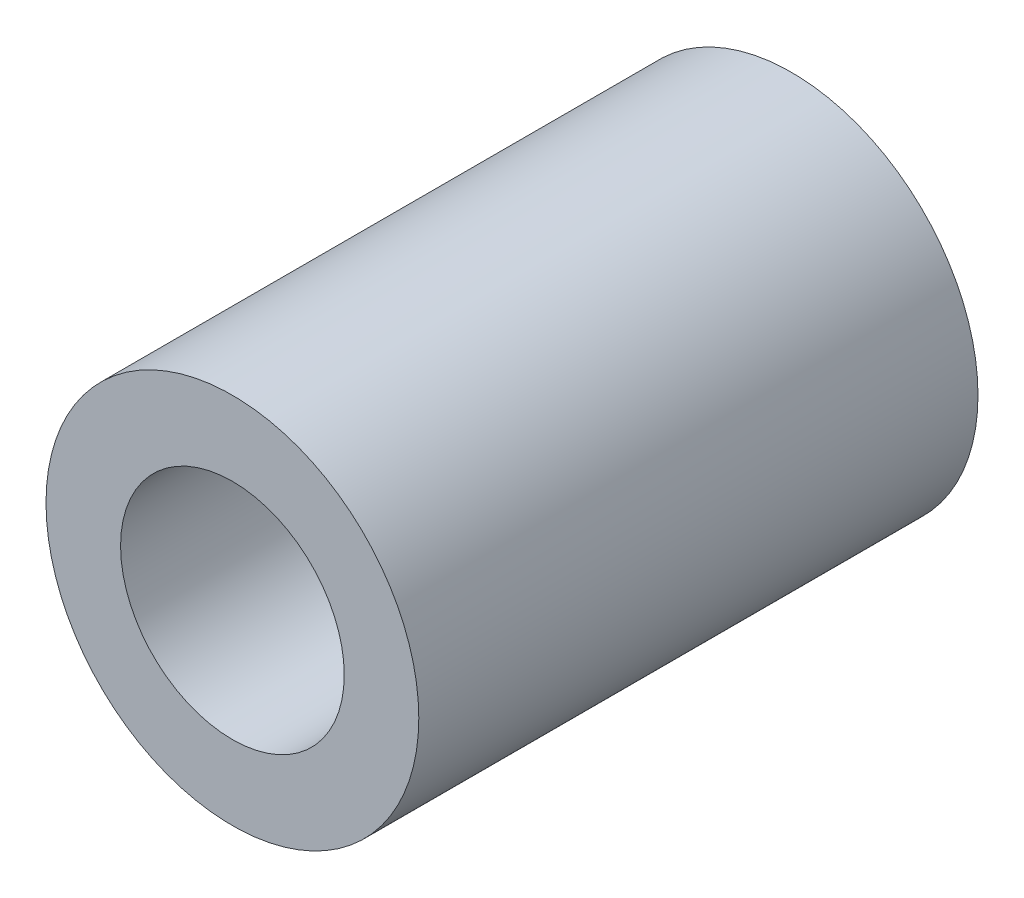
SolidWorks part; units mm, degrees
ref_plane "Plan de face" through (0, 0, 0) normal (0, 0, 1) x (1, 0, 0)
ref_plane "Plan de dessus" through (0, 0, 0) normal (0, 1, 0) x (1, 0, 0)
ref_plane "Plan de droite" through (0, 0, 0) normal (1, 0, 0) x (0, 0, -1)
sketch "Esquisse1" plane through (0, 0, 0) normal (0, 0, 1) x (1, 0, 0)
  circle A0 centre (0, 0) radius 1.2
  circle A1 centre (0, 0) radius 2
  dimension "D1" = 4
  dimension "D2" = 2.4
extrude "Boss.-Extru.1" add sketch "Esquisse1" along normal blind 6
